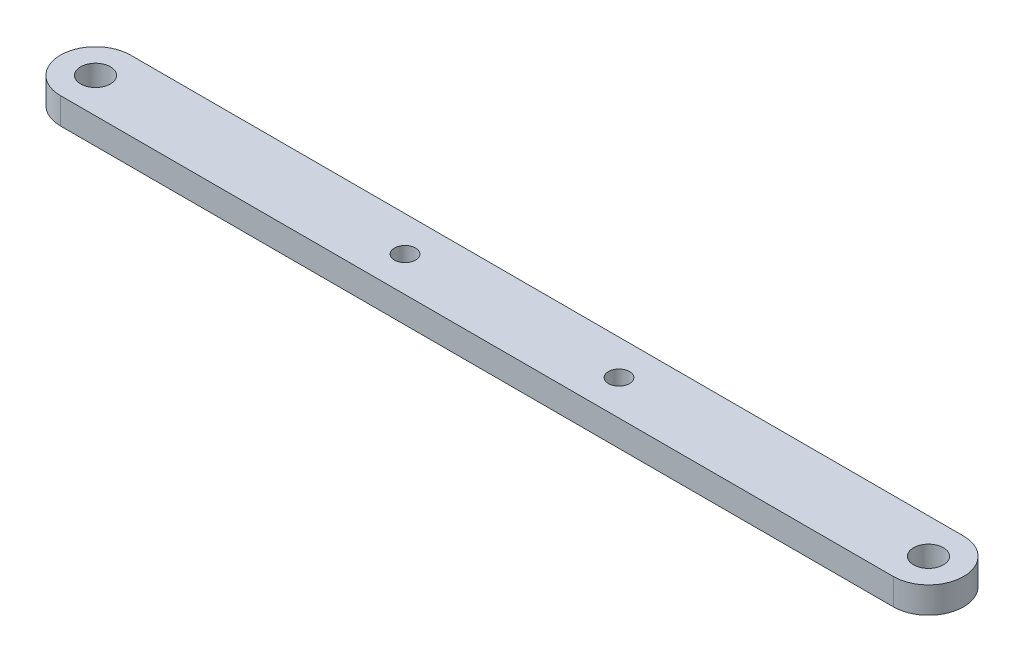
SolidWorks part; units mm, degrees
ref_plane "Front Plane" through (0, 0, 0) normal (0, 0, 1) x (1, 0, 0)
ref_plane "Top Plane" through (0, 0, 0) normal (0, 1, 0) x (1, 0, 0)
ref_plane "Right Plane" through (0, 0, 0) normal (1, 0, 0) x (0, 0, -1)
sketch "Sketch1" plane through (0, 0, 0) normal (0, 1, 0) x (1, 0, 0)
  line L0 (0, 0) -> (95, 0) construction
  line L1 (0, 4) -> (95, 4)
  line L2 (0, -4) -> (95, -4)
  arc A0 (0, 4) -> (0, -4) centre (0, 0) ccw
  arc A1 (95, -4) -> (95, 4) centre (95, 0) ccw
  point P3 (47.5, 0)
  dimension "D1" = 95
  dimension "D2" = 8
extrude "Boss-Extrude1" add sketch "Sketch1" along normal blind 3
hole_wizard "M3 Clearance Hole1" positions "Sketch3" profile "Sketch4" hole size "M3" standard "ANSI Metric" end condition through all
sketch "Sketch3" plane through (0, 3, 0) normal (0, 1, 0) x (1, 0, 0)
  point P0 (95, 0)
  point P3 (0, 0)
sketch "Sketch4" plane through (95, 3, 0) normal (1, 0, 0) x (0, 0, 1)
  line L0 (0, 0) -> (0, 3)
  line L1 (0, 3) -> (1.7, 3)
  line L2 (1.7, 3) -> (1.7, 0)
  line L5 (1.7, 0) -> (0, 0)
  line L11 (0, -6.35) -> (0, 107.95) construction
  dimension "Thru Hole Dia." = 3.4
  dimension "Thru Hole Depth" = 3
hole_wizard "M2 Clearance Hole1" positions "Sketch6" profile "Sketch5" hole size "M2" standard "ANSI Metric" end condition through all
sketch "Sketch6" plane through (0, 3, 0) normal (0, 1, 0) x (1, 0, 0)
  line L3 (-4, 0) -> (99, 0) construction
  line L8 (35.3, 0) -> (47.5, 0) construction
  line L9 (47.5, 0) -> (59.7, 0) construction
  arc A0 (0, 4) -> (0, -4) centre (0, 0) ccw construction
  arc A1 (95, -4) -> (95, 4) centre (95, 0) ccw construction
  point P0 (59.7, 0)
  point P2 (35.3, 0)
  dimension "D1" = 12.2
  dimension "D2" = 12.2
sketch "Sketch5" plane through (59.7, 3, 0) normal (1, 0, 0) x (0, 0, 1)
  line L0 (0, 0) -> (0, 3)
  line L1 (0, 3) -> (1.2, 3)
  line L2 (1.2, 3) -> (1.2, 0)
  line L5 (1.2, 0) -> (0, 0)
  line L11 (0, -6.35) -> (0, 107.95) construction
  dimension "Thru Hole Dia." = 2.4
  dimension "Thru Hole Depth" = 3
